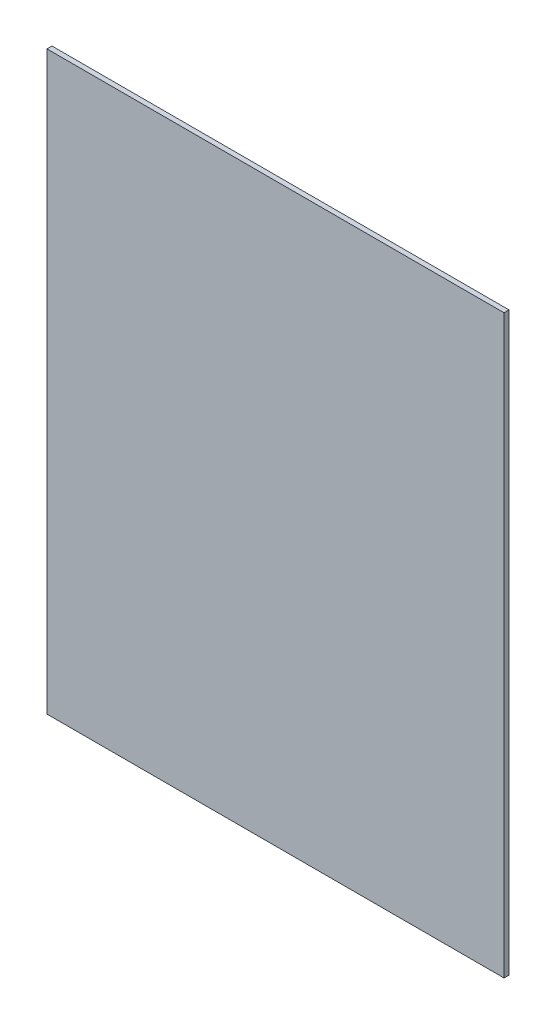
SolidWorks part; units mm, degrees
material "Acrílico (Impacto medio-alto)"
ref_plane "Alzado" through (0, 0, 0) normal (0, 0, 1) x (1, 0, 0)
ref_plane "Planta" through (0, 0, 0) normal (0, 1, 0) x (1, 0, 0)
ref_plane "Vista lateral" through (0, 0, 0) normal (1, 0, 0) x (0, 0, -1)
sketch "Croquis1" plane through (0, 0, 0) normal (0, 1, 0) x (1, 0, 0)
  line L1 (119, 1.3) -> (-119, 1.3)
  line L2 (119, 1.3) -> (119, -1.3)
  line L3 (119, -1.3) -> (-119, -1.3)
  line L4 (-119, 1.3) -> (-119, -1.3)
  line L5 (119, 1.3) -> (-119, -1.3) construction
  line L6 (119, -1.3) -> (-119, 1.3) construction
  point P0 (0, 0)
  dimension "D1" = 238
  dimension "D2" = 2.6
extrude "Saliente-Extruir1" add sketch "Croquis1" along normal blind 300
